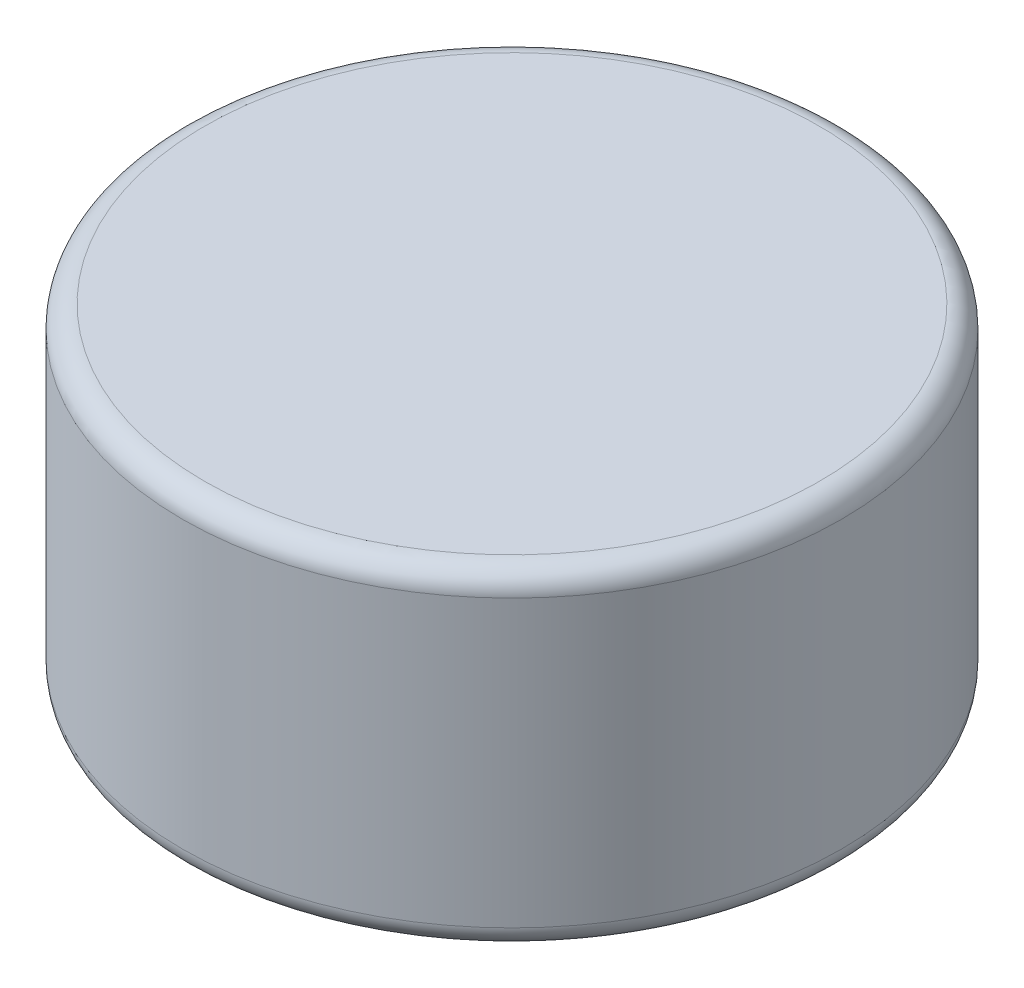
SolidWorks part; units mm, degrees
ref_plane "Front Plane" through (0, 0, 0) normal (0, 0, 1) x (1, 0, 0)
ref_plane "Top Plane" through (0, 0, 0) normal (0, 1, 0) x (1, 0, 0)
ref_plane "Right Plane" through (0, 0, 0) normal (1, 0, 0) x (0, 0, -1)
sketch "Sketch1" plane through (0, 0, 0) normal (0, 1, 0) x (1, 0, 0)
  circle A0 centre (0, 0) radius 3
extrude "Boss-Extrude1" add sketch "Sketch1" along normal blind 3
fillet "Fillet1" radius 0.2 2 edges at (0, 0, 3) (0, 3, 3)
